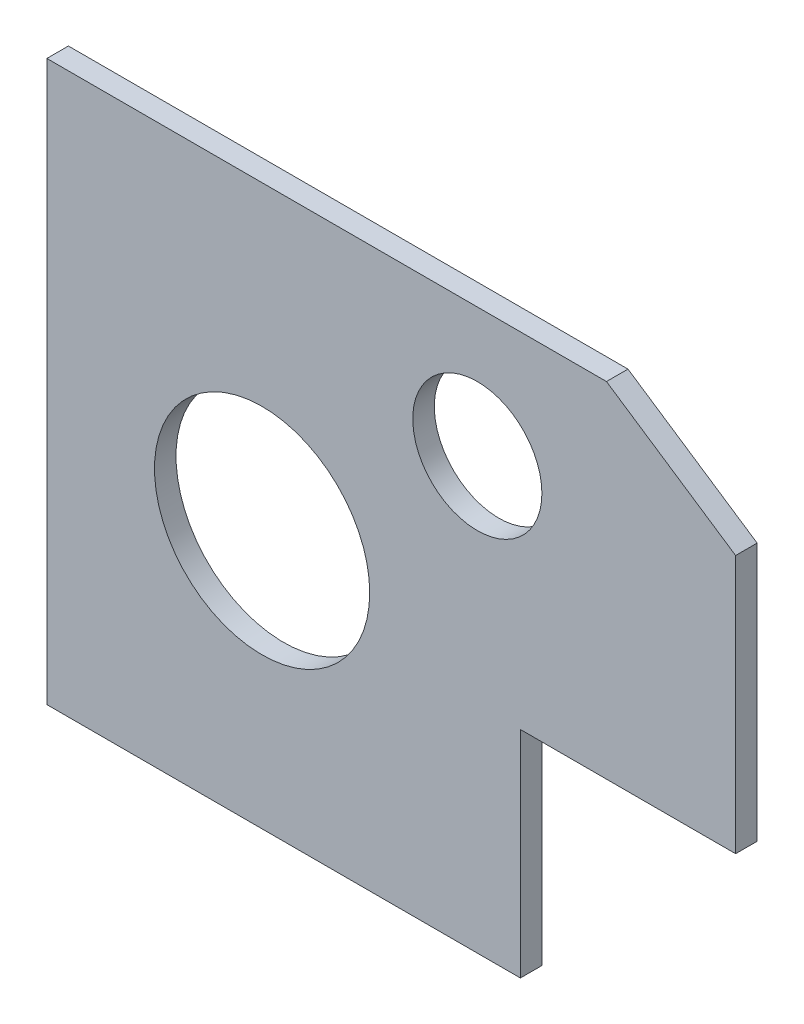
SolidWorks part; units mm, degrees
ref_plane "Front Plane" through (0, 0, 0) normal (0, 0, 1) x (1, 0, 0)
ref_plane "Top Plane" through (0, 0, 0) normal (0, 1, 0) x (1, 0, 0)
ref_plane "Right Plane" through (0, 0, 0) normal (1, 0, 0) x (0, 0, -1)
sketch "Sketch1" plane through (0, 0, 0) normal (0, 0, 1) x (1, 0, 0)
  line L0 (0, 63.5) -> (-63.5, 63.5)
  line L1 (-63.5, 63.5) -> (-63.5, 0)
  line L2 (-63.5, 0) -> (-203.2, 0)
  line L3 (-203.2, 0) -> (-203.2, 165.1)
  line L4 (-203.2, 165.1) -> (-38.1, 165.1)
  line L5 (-38.1, 165.1) -> (0, 139.7)
  line L6 (0, 139.7) -> (0, 63.5)
  circle A0 centre (-76.2, 127) radius 19.05
  circle A1 centre (-139.7, 76.2) radius 31.75
  point P12 (0, 0)
  point P13 (0, 0)
  point P14 (0, 0)
  dimension "D6" = 38.1
  dimension "D12" = 63.5
  dimension "D2" = 203.2
  dimension "D3" = 63.5
  dimension "D4" = 63.5
  dimension "D5" = 127
  dimension "D7" = 38.1
  dimension "D8" = 76.2
  dimension "D9" = 63.5
  dimension "D10" = 165.1
  dimension "D11" = 139.7
  dimension "D13" = 165.1
  dimension "D14" = 38.1
  dimension "D15" = 76.2
extrude "Boss-Extrude1" add sketch "Sketch1" along normal blind 6.35
